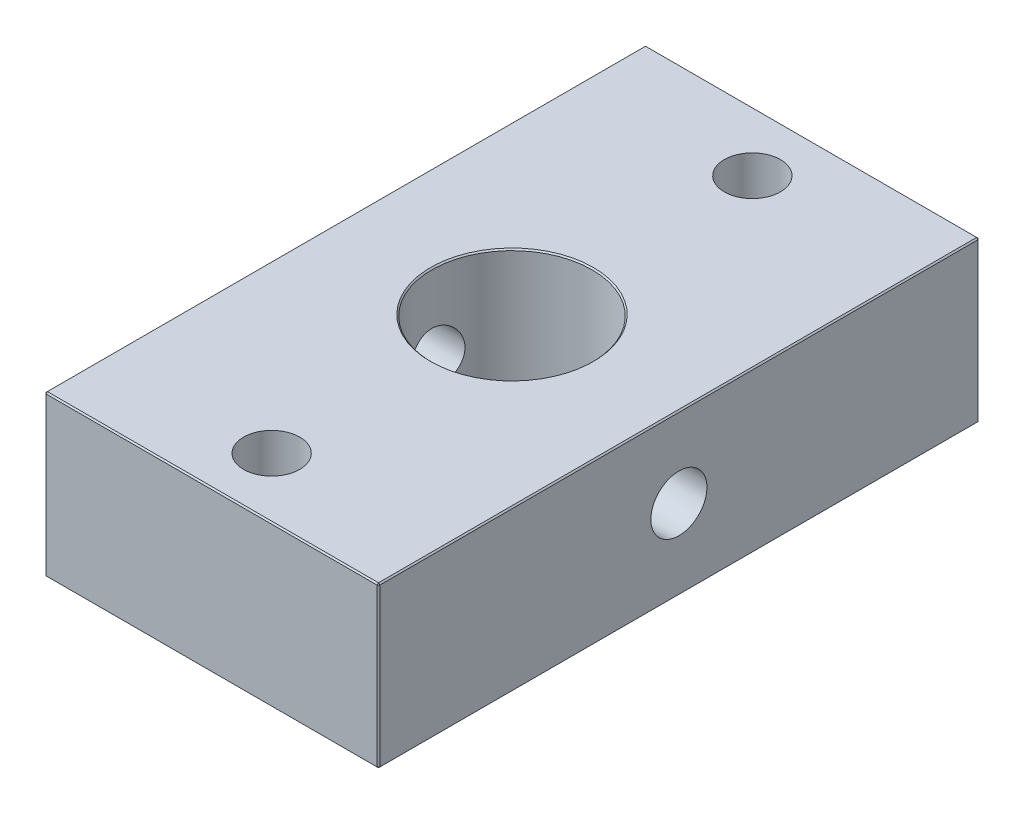
SolidWorks part; units mm, degrees
ref_plane "Front Plane" through (0, 0, 0) normal (0, 0, 1) x (1, 0, 0)
ref_plane "Top Plane" through (0, 0, 0) normal (0, 1, 0) x (1, 0, 0)
ref_plane "Right Plane" through (0, 0, 0) normal (1, 0, 0) x (0, 0, -1)
sketch "Sketch1" plane through (0, 0, 0) normal (0, 1, 0) x (1, 0, 0)
  line L1 (-12.5, -22.5) -> (12.5, -22.5)
  line L2 (-12.5, -22.5) -> (-12.5, 22.5)
  line L3 (-12.5, 22.5) -> (12.5, 22.5)
  line L4 (12.5, -22.5) -> (12.5, 22.5)
  line L5 (-12.5, -22.5) -> (12.5, 22.5) construction
  line L6 (-12.5, 22.5) -> (12.5, -22.5) construction
  circle A0 centre (0, 0) radius 6
  point P0 (0, 0)
  dimension "D1" = 25
  dimension "D2" = 45
extrude "Boss-Extrude1" add sketch "Sketch1" along normal blind 12
hole_wizard "M5 Tapped Hole2" positions "Sketch4" profile "Sketch5" tap size "M5" standard "DIN" end condition through all
sketch "Sketch4" plane through (0, 12, 0) normal (0, 1, 0) x (1, 0, 0)
  point P0 (0, 18)
  point P2 (0, -18)
  dimension "D1" = 18
  dimension "D2" = 18
sketch "Sketch5" plane through (0, 12, -18) normal (1, 0, 0) x (0, 0, 1)
  line L0 (0, 0) -> (0, 12)
  line L1 (0, 12) -> (2.1, 12)
  line L2 (2.1, 12) -> (2.1, 0)
  line L5 (2.1, 0) -> (0, 0)
  line L11 (0, -6.35) -> (0, 107.95) construction
  dimension "Thru Tap Drill Dia." = 4.2
  dimension "Thru Tap Drill Depth" = 12
cosmetic thread "Hole Thread3" parameters "D2"=5
cosmetic thread "Hole Thread4" parameters "D2"=5
hole_wizard "M5 Tapped Hole3" positions "Sketch6" profile "Sketch7" tap size "M5" standard "DIN" end condition through all
sketch "Sketch6" plane through (-12.5, 0, 0) normal (-1, 0, 0) x (0, 0, 1)
  line L0 (-22.5, 12) -> (22.5, 12) construction
  line L2 (-22.5, 12) -> (-22.5, 0) construction
  point P0 (0, 6)
  point P9 (22.5, 2.7194)
  dimension "D1" = 6
  dimension "D2" = 22.5
sketch "Sketch7" plane through (-12.5, 6, 0) normal (0, 1, 0) x (0, 0, 1)
  line L0 (0, 0) -> (0, 25)
  line L1 (0, 25) -> (2.1, 25)
  line L2 (2.1, 25) -> (2.1, 0)
  line L5 (2.1, 0) -> (0, 0)
  line L11 (0, -6.35) -> (0, 107.95) construction
  dimension "Thru Tap Drill Dia." = 4.2
  dimension "Thru Tap Drill Depth" = 25
cosmetic thread "Hole Thread5" parameters "D2"=5
chamfer "Chamfer1" distance 0.1 angle 45 14 edges at (0, 0, 6) (0, 12, 6) (0, 0, 22.5) (12.5, 6, 22.5) (12.5, 0, 0) (-12.5, 6, 22.5) (-12.5, 0, 0) (0, 12, 22.5) (-12.5, 12, 0) (12.5, 12, 0) (-12.5, 6, -22.5) (0, 12, -22.5) (12.5, 6, -22.5) (0, 0, -22.5)
